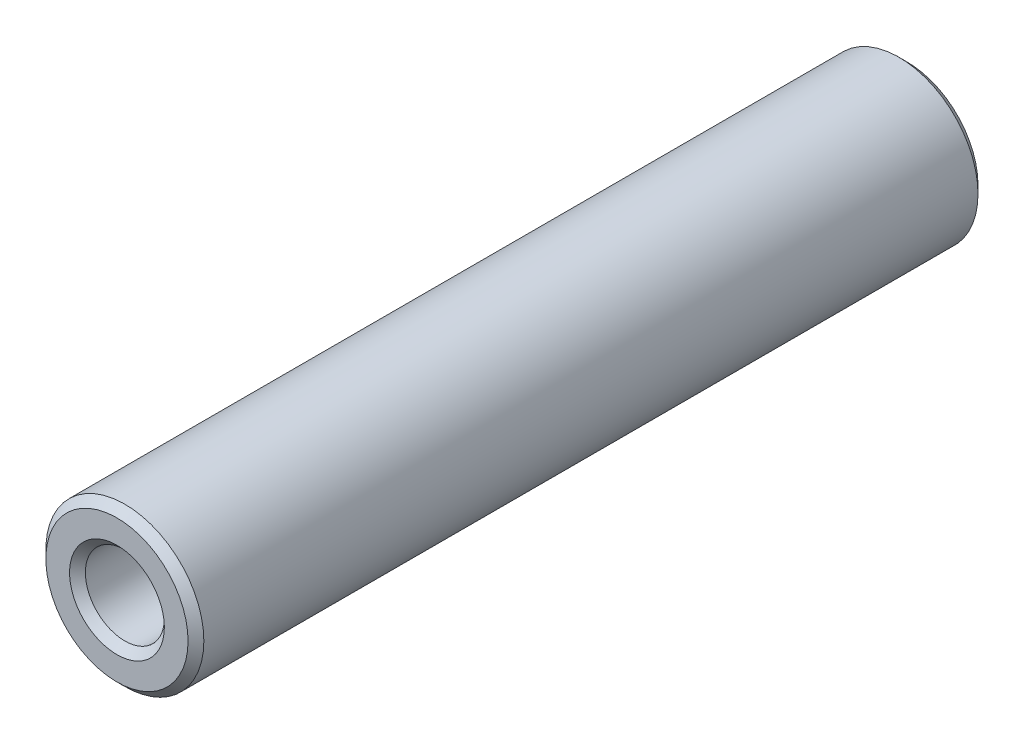
SolidWorks part; units mm, degrees
ref_plane "Спереди" through (0, 0, 0) normal (0, 0, 1) x (1, 0, 0)
ref_plane "Сверху" through (0, 0, 0) normal (0, 1, 0) x (1, 0, 0)
ref_plane "Справа" through (0, 0, 0) normal (1, 0, 0) x (0, 0, -1)
sketch "Эскиз1" plane through (0, 0, 0) normal (0, 0, 1) x (1, 0, 0)
  circle A0 centre (0, 0) radius 1
  circle A1 centre (0, 0) radius 2
extrude "Бобышка-Вытянуть1" add sketch "Эскиз1" along normal blind 20
chamfer "Фаска1" distance 0.2 angle 45 4 edges at (1, 0, 0) (2, 0, 0) (1, 0, 20) (2, 0, 20)
